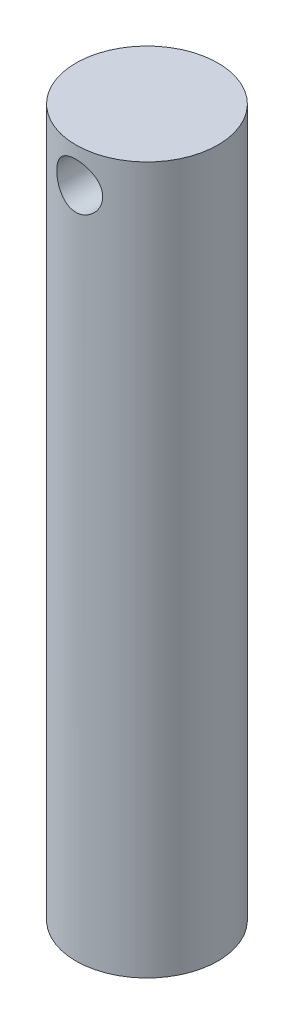
SolidWorks part; units mm, degrees
ref_plane "Front Plane" through (0, 0, 0) normal (0, 0, 1) x (1, 0, 0)
ref_plane "Top Plane" through (0, 0, 0) normal (0, 1, 0) x (1, 0, 0)
ref_plane "Right Plane" through (0, 0, 0) normal (1, 0, 0) x (0, 0, -1)
sketch "Sketch1" plane through (0, 0, 0) normal (0, 1, 0) x (1, 0, 0)
  circle A0 centre (0, 0) radius 10.05
  dimension "D1" = 20.1
extrude "Boss-Extrude1" add sketch "Sketch1" along normal blind 100
sketch "Sketch2" plane through (0, 0, 0) normal (0, 0, 1) x (1, 0, 0)
  line L0 (10.05, 100) -> (-10.05, 100) construction
  line L1 (-10.05, 100) -> (-10.05, 0) construction
  circle A0 centre (0, 95) radius 3.25
  dimension "D1" = 6.5
  dimension "D2" = 5
  dimension "D3" = 10.05
extrude "Cut-Extrude1" cut sketch "Sketch2" against normal through all both and the other way through all
